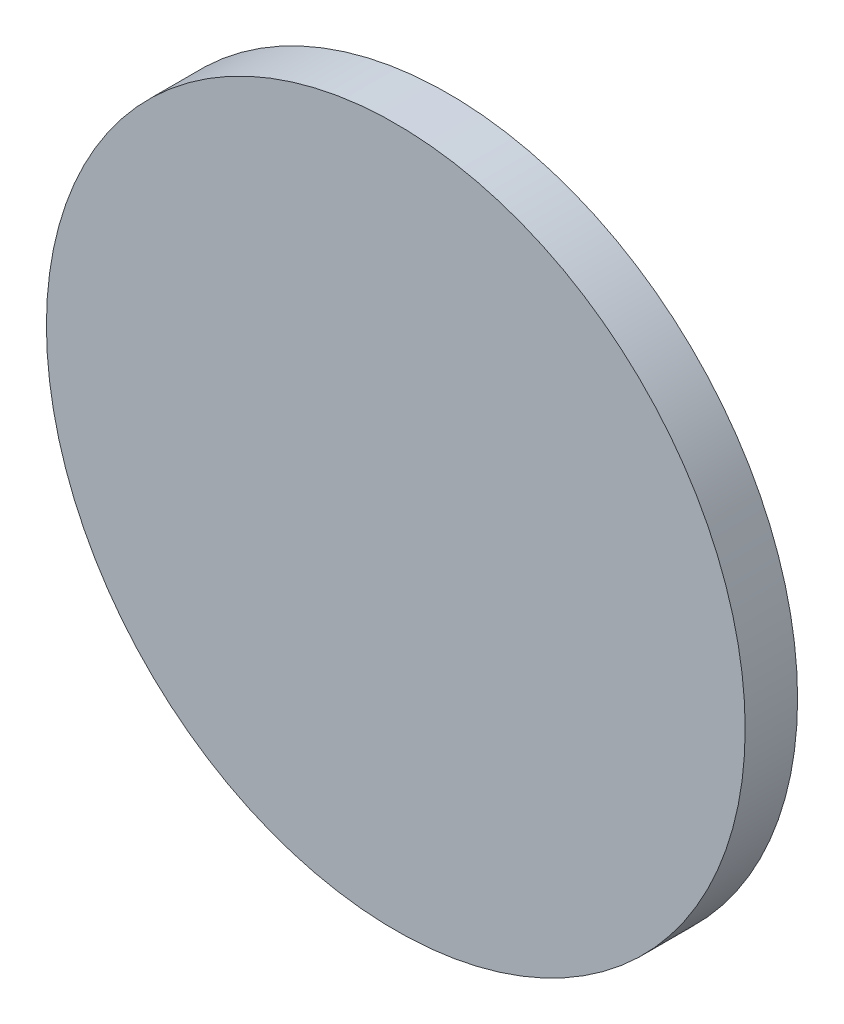
SolidWorks part; units mm, degrees
ref_plane "前视基准面" through (0, 0, 0) normal (0, 0, 1) x (1, 0, 0)
ref_plane "上视基准面" through (0, 0, 0) normal (0, 1, 0) x (1, 0, 0)
ref_plane "右视基准面" through (0, 0, 0) normal (1, 0, 0) x (0, 0, -1)
sketch "草图1" plane through (0, 0, 0) normal (0, 0, 1) x (1, 0, 0)
  circle A0 centre (0, 0) radius 20
  dimension "D1" = 40
extrude "凸台-拉伸1" add sketch "草图1" along normal blind 3 contours A0
